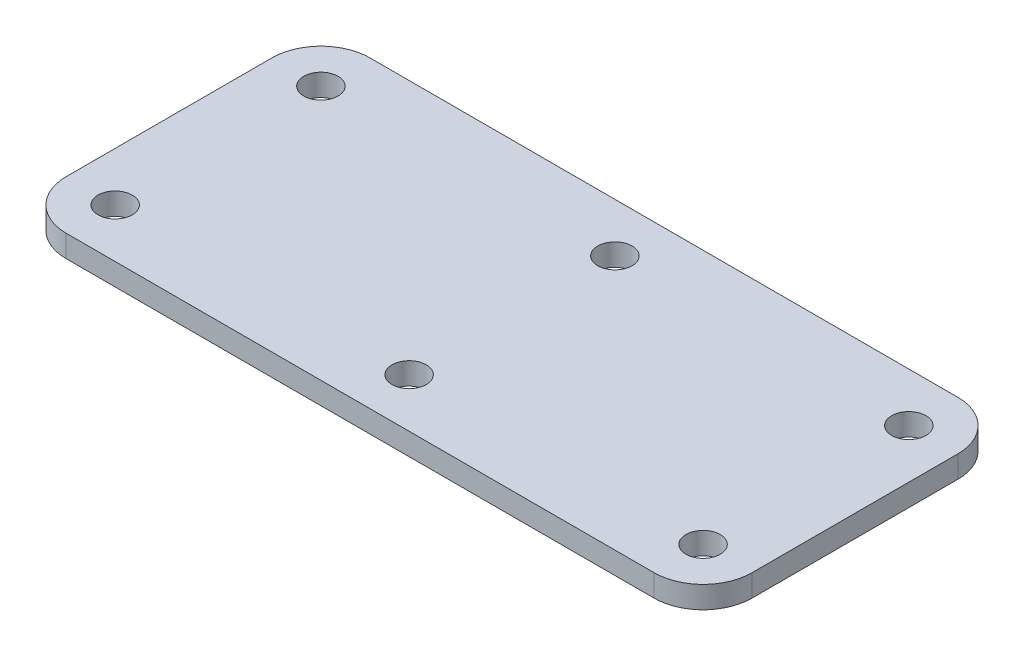
SolidWorks part; units mm, degrees
ref_plane "Front" through (0, 0, 0) normal (0, 0, 1) x (1, 0, 0)
ref_plane "Top" through (0, 0, 0) normal (0, 1, 0) x (1, 0, 0)
ref_plane "Right" through (0, 0, 0) normal (1, 0, 0) x (0, 0, -1)
sketch "Sketch1" plane through (0, 0, 0) normal (0, 1, 0) x (1, 0, 0)
  line L1 (-23.733, -543.1502) -> (96.267, -543.1502)
  line L2 (-33.733, -553.1502) -> (-33.733, -595.1502)
  line L3 (-23.733, -605.1502) -> (96.267, -605.1502)
  line L4 (106.267, -553.1502) -> (106.267, -595.1502)
  arc A0 (-33.733, -595.1502) -> (-23.733, -605.1502) centre (-23.733, -595.1502) ccw
  arc A1 (96.267, -605.1502) -> (106.267, -595.1502) centre (96.267, -595.1502) ccw
  arc A2 (96.267, -543.1502) -> (106.267, -553.1502) centre (96.267, -553.1502) cw
  arc A3 (-23.733, -543.1502) -> (-33.733, -553.1502) centre (-23.733, -553.1502) ccw
  circle A4 centre (36.267, -553.1502) radius 3.5
  circle A5 centre (96.267, -553.1502) radius 3.5
  circle A6 centre (-23.733, -553.1502) radius 3.5
  circle A7 centre (-23.733, -595.1502) radius 3.5
  circle A8 centre (96.267, -595.1502) radius 3.5
  circle A9 centre (36.267, -595.1502) radius 3.5
  dimension "D1" = 10
  dimension "D2" = 10
  dimension "D3" = 10
  dimension "D4" = 60
  dimension "D5" = 140
extrude "Boss-Extrude1" add sketch "Sketch1" along normal blind 4.5
